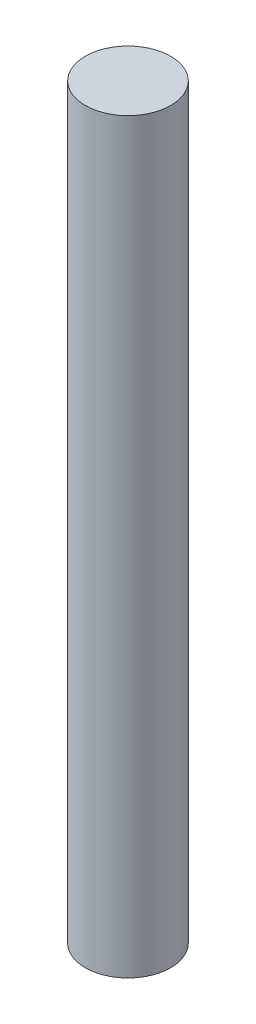
SolidWorks part; units mm, degrees
ref_plane "Ön Düzlem" through (0, 0, 0) normal (0, 0, 1) x (1, 0, 0)
ref_plane "Üst Düzlem" through (0, 0, 0) normal (0, 1, 0) x (1, 0, 0)
ref_plane "Sağ Düzlem" through (0, 0, 0) normal (1, 0, 0) x (0, 0, -1)
sketch "Sketch1" plane through (0, 0, 0) normal (0, 1, 0) x (1, 0, 0)
  circle A0 centre (0, 0) radius 4
  dimension "D1" = 8
extrude "Boss-Extrude1" add sketch "Sketch1" along normal blind 70
